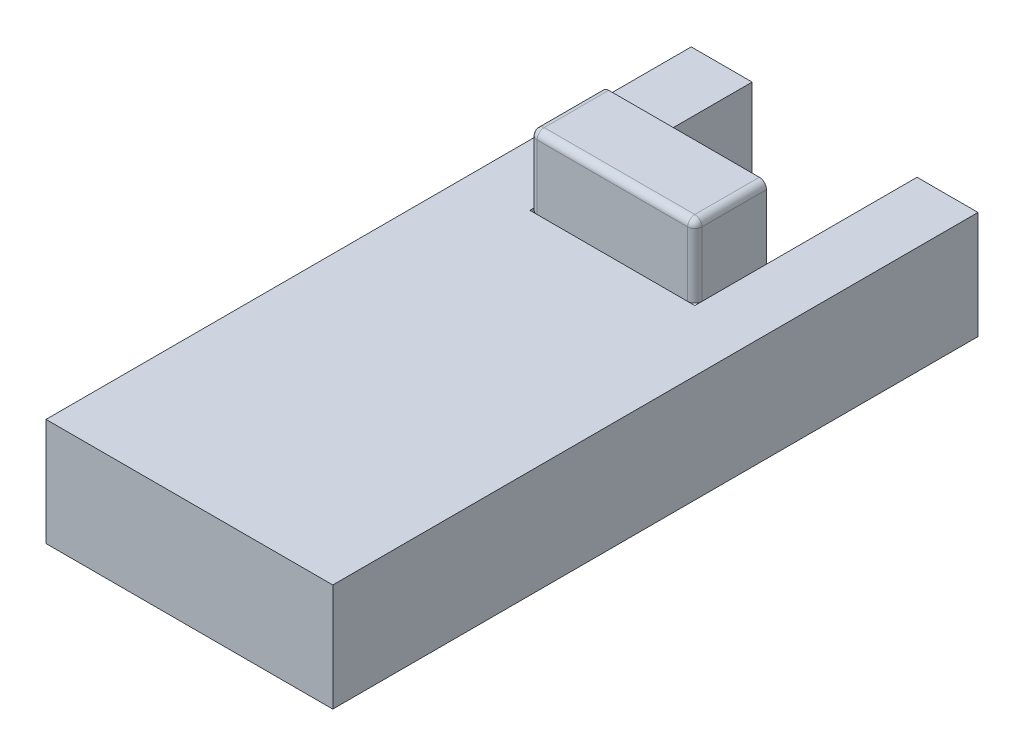
SolidWorks part; units mm, degrees
ref_plane "Alzado" through (0, 0, 0) normal (0, 0, 1) x (1, 0, 0)
ref_plane "Planta" through (0, 0, 0) normal (0, 1, 0) x (1, 0, 0)
ref_plane "Vista lateral" through (0, 0, 0) normal (1, 0, 0) x (0, 0, -1)
sketch "Croquis2" plane through (0, 0, 0) normal (0, 1, 0) x (1, 0, 0)
  line L1 (200, -450) -> (-200, -450)
  line L2 (200, -450) -> (200, 450)
  line L3 (200, 450) -> (-200, 450)
  line L4 (-200, -450) -> (-200, 450)
  line L5 (200, -450) -> (-200, 450) construction
  line L6 (200, 450) -> (-200, -450) construction
  point P0 (0, 0)
  dimension "D1" = 900
  dimension "D2" = 400
extrude "Saliente-Extruir1" add sketch "Croquis2" along normal blind 150
sketch "Croquis3" plane through (0, 0, 0) normal (0, -1, 0) x (1, 0, 0)
  line L0 (200, -450) -> (-200, -450) construction
  line L1 (-115, -760) -> (115, -760)
  line L2 (-115, -760) -> (-115, -140)
  line L3 (-115, -140) -> (115, -140)
  line L4 (115, -760) -> (115, -140)
  line L5 (-115, -760) -> (115, -140) construction
  line L6 (-115, -140) -> (115, -760) construction
  point P0 (0, -450)
  dimension "D1" = 230
  dimension "D2" = 310
extrude "Cortar-Extruir1" cut sketch "Croquis3" against normal blind 150
sketch "Croquis9" plane through (0, 150, 0) normal (0, 1, 0) x (1, 0, 0)
  line L0 (115, 450) -> (115, 140) construction
  line L5 (-115, 140) -> (115, 140)
  line L6 (-115, 140) -> (-115, 240)
  line L7 (-115, 240) -> (115, 240)
  line L8 (115, 140) -> (115, 240)
  dimension "D1" = 100
extrude "Saliente-Extruir6" add sketch "Croquis9" along normal blind 100 separate body
fillet "Redondeo1" radius 10 1 edges at (-115, 250, -190)
fillet "Redondeo2" radius 10 3 edges at (-115, 195, -140) (5, 250, -140) (-112.0711, 247.0711, -140)
fillet "Redondeo3" radius 10 3 edges at (115, 195, -140) (115, 250, -195) (115, 247.0711, -142.9289)
